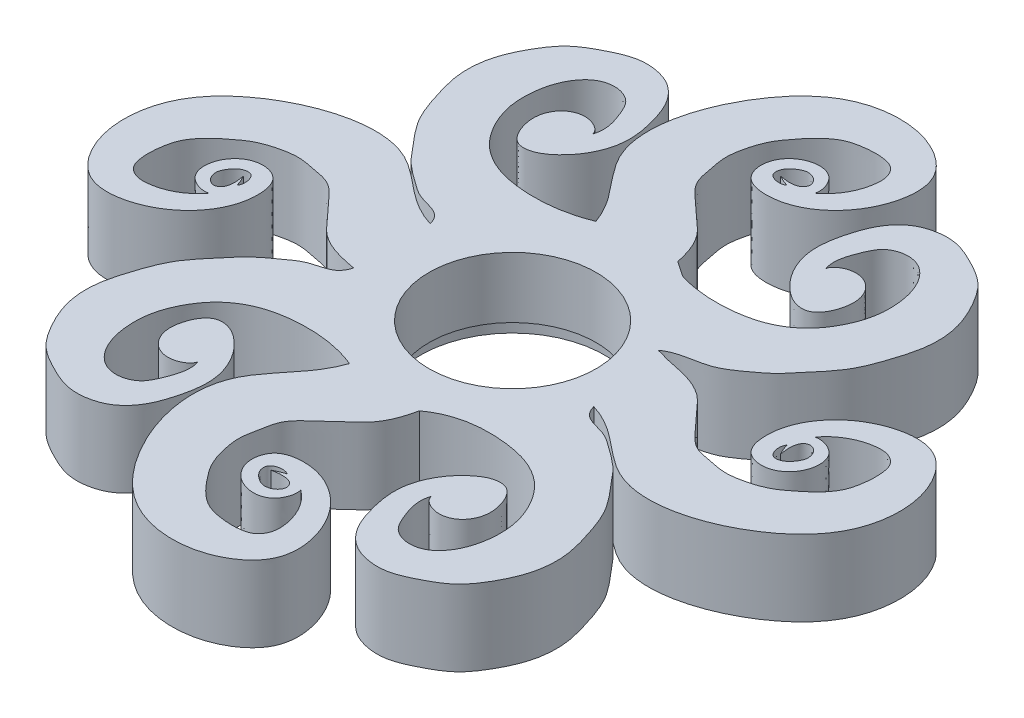
SolidWorks part; units mm, degrees
ref_plane "Front Plane" through (0, 0, 0) normal (0, 0, 1) x (1, 0, 0)
ref_plane "Top Plane" through (0, 0, 0) normal (0, 1, 0) x (1, 0, 0)
ref_plane "Right Plane" through (0, 0, 0) normal (1, 0, 0) x (0, 0, -1)
sketch "Sketch1" plane through (0, 0, 0) normal (0, 1, 0) x (1, 0, 0)
  line L0 (-137.5221, 312.9661) -> (42.0831, 492.5712) construction
  line L1 (0, 0) -> (100, 0)
  line L2 (0, 0) -> (0, 100)
  line L3 (0, 100) -> (100, 100)
  line L4 (100, 0) -> (100, 100)
  line L5 (0, 50) -> (100, 50) construction
  line L6 (50, 100) -> (50, 0) construction
  line L7 (0, 0) -> (100, 0)
  line L8 (0, 100) -> (100, 100)
  line L9 (0, 0) -> (100, 100)
  line L10 (0, 100) -> (100, 0)
  circle A0 centre (50, 50) radius 11
  spline S0 degree 3 poles (41.8661, 57.4054) (46.701, 61.1096) (45.1353, 68.2538) (35.8651, 77.0149) (39.534, 89.8969) (48.042, 98.1531) (57.0489, 98.3656) (63.2707, 93.2329) (62.2719, 86.5125) (58.4841, 81.8528) (53.9618, 80.0775) (49.6945, 80.8153) (48.8956, 84.5821) (51.2739, 87.369) (56.7979, 87.4647) (56.8692, 80.8999) (51.8214, 83.52) knots 0 0 0 0 0.130846 0.205908 0.373668 0.458524 0.563429 0.616002 0.684327 0.743989 0.794856 0.830051 0.857944 0.89521 0.928487 1 1 1 1
  spline S1 degree 3 poles (51.8214, 83.52) (52.472, 83.4079) (53.4015, 83.2628) (54.5829, 83.6983) (54.8837, 84.4198) (54.6621, 85.0586) (54.2169, 85.5067) (53.6439, 85.7228) (53.0512, 85.8036) (52.3837, 85.5614) (51.6885, 85.0892) (51.053, 84.3727) (50.8497, 82.6835) (52.804, 82.495) (53.2799, 82.9075) knots 0 0 0 0 0.166366 0.241726 0.299227 0.344909 0.407108 0.454045 0.499649 0.556761 0.630203 0.713357 0.798618 1 1 1 1
  spline S2 degree 3 poles (56.0389, 83.8395) (57.6208, 85.0131) (58.9873, 87.4073) (59.0345, 90.5343) (58.0896, 91.9736) (56.2517, 92.4492) (54.2472, 92.3528) (52.0283, 91.9307) (50.1178, 90.5672) (48.5985, 88.7801) (47.0469, 86.6832) (46.326, 84.3273) (45.9316, 81.9129) (46.4498, 79.6692) (46.8136, 77.1078) (48.8758, 75.2303) (50.9325, 73.3151) (53.6539, 71.081) (54.6991, 67.8956) (55.1151, 65.2419) (55.889, 63.2218) (55.1431, 59.3575) (58.2485, 58.4927) (59.1083, 56.1675) knots 0 0 0 0 0.103134 0.133672 0.160055 0.18614 0.228667 0.265873 0.302526 0.349029 0.389123 0.438157 0.476951 0.515573 0.558652 0.60831 0.655131 0.7086 0.789325 0.822647 0.849802 0.902946 1 1 1 1
  spline S3 degree 3 poles (56.0389, 16.1605) (57.6208, 14.9869) (58.9873, 12.5927) (59.0345, 9.4657) (58.0896, 8.0264) (56.2517, 7.5508) (54.2472, 7.6472) (52.0283, 8.0693) (50.1178, 9.4328) (48.5985, 11.2199) (47.0469, 13.3168) (46.326, 15.6727) (45.9316, 18.0871) (46.4498, 20.3308) (46.8136, 22.8922) (48.8758, 24.7697) (50.9325, 26.6849) (53.6539, 28.919) (54.6991, 32.1044) (55.1151, 34.7581) (55.889, 36.7782) (55.1431, 40.6425) (58.2485, 41.5073) (59.1083, 43.8325) knots 0 0 0 0 0.103134 0.133672 0.160055 0.18614 0.228667 0.265873 0.302526 0.349029 0.389123 0.438157 0.476951 0.515573 0.558652 0.60831 0.655131 0.7086 0.789325 0.822647 0.849802 0.902946 1 1 1 1
  spline S4 degree 3 poles (51.8214, 16.48) (52.472, 16.5921) (53.4015, 16.7372) (54.5829, 16.3017) (54.8837, 15.5802) (54.6621, 14.9414) (54.2169, 14.4933) (53.6439, 14.2772) (53.0512, 14.1964) (52.3837, 14.4386) (51.6885, 14.9108) (51.053, 15.6273) (50.8497, 17.3165) (52.804, 17.505) (53.2799, 17.0925) knots 0 0 0 0 0.166366 0.241726 0.299227 0.344909 0.407108 0.454045 0.499649 0.556761 0.630203 0.713357 0.798618 1 1 1 1
  spline S5 degree 3 poles (41.8661, 42.5946) (46.701, 38.8904) (45.1353, 31.7462) (35.8651, 22.9851) (39.534, 10.1031) (48.042, 1.8469) (57.0489, 1.6344) (63.2707, 6.7671) (62.2719, 13.4875) (58.4841, 18.1472) (53.9618, 19.9225) (49.6945, 19.1847) (48.8956, 15.4179) (51.2739, 12.631) (56.7979, 12.5353) (56.8692, 19.1001) (51.8214, 16.48) knots 0 0 0 0 0.130846 0.205908 0.373668 0.458524 0.563429 0.616002 0.684327 0.743989 0.794856 0.830051 0.857944 0.89521 0.928487 1 1 1 1
  spline S6 degree 3 poles (83.8395, 56.0389) (85.0131, 57.6208) (87.4073, 58.9873) (90.5343, 59.0345) (91.9736, 58.0896) (92.4492, 56.2517) (92.3528, 54.2472) (91.9307, 52.0283) (90.5672, 50.1178) (88.7801, 48.5985) (86.6832, 47.0469) (84.3273, 46.326) (81.9129, 45.9316) (79.6692, 46.4498) (77.1078, 46.8136) (75.2303, 48.8758) (73.3151, 50.9325) (71.081, 53.6539) (67.8956, 54.6991) (65.2419, 55.1151) (63.2218, 55.889) (59.3575, 55.1431) (58.4927, 58.2485) (56.1675, 59.1083) knots 0 0 0 0 0.103134 0.133672 0.160055 0.18614 0.228667 0.265873 0.302526 0.349029 0.389123 0.438157 0.476951 0.515573 0.558652 0.60831 0.655131 0.7086 0.789325 0.822647 0.849802 0.902946 1 1 1 1
  spline S7 degree 3 poles (83.52, 51.8214) (83.4079, 52.472) (83.2628, 53.4015) (83.6983, 54.5829) (84.4198, 54.8837) (85.0586, 54.6621) (85.5067, 54.2169) (85.7228, 53.6439) (85.8036, 53.0512) (85.5614, 52.3837) (85.0892, 51.6885) (84.3727, 51.053) (82.6835, 50.8497) (82.495, 52.804) (82.9075, 53.2799) knots 0 0 0 0 0.166366 0.241726 0.299227 0.344909 0.407108 0.454045 0.499649 0.556761 0.630203 0.713357 0.798618 1 1 1 1
  spline S8 degree 3 poles (57.4054, 41.8661) (61.1096, 46.701) (68.2538, 45.1353) (77.0149, 35.8651) (89.8969, 39.534) (98.1531, 48.042) (98.3656, 57.0489) (93.2329, 63.2707) (86.5125, 62.2719) (81.8528, 58.4841) (80.0775, 53.9618) (80.8153, 49.6945) (84.5821, 48.8956) (87.369, 51.2739) (87.4647, 56.7979) (80.8999, 56.8692) (83.52, 51.8214) knots 0 0 0 0 0.130846 0.205908 0.373668 0.458524 0.563429 0.616002 0.684327 0.743989 0.794856 0.830051 0.857944 0.89521 0.928487 1 1 1 1
  spline S9 degree 3 poles (16.1605, 43.9611) (14.9869, 42.3792) (12.5927, 41.0127) (9.4657, 40.9655) (8.0264, 41.9104) (7.5508, 43.7483) (7.6472, 45.7528) (8.0693, 47.9717) (9.4328, 49.8822) (11.2199, 51.4015) (13.3168, 52.9531) (15.6727, 53.674) (18.0871, 54.0684) (20.3308, 53.5502) (22.8922, 53.1864) (24.7697, 51.1242) (26.6849, 49.0675) (28.919, 46.3461) (32.1044, 45.3009) (34.7581, 44.8849) (36.7782, 44.111) (40.6425, 44.8569) (41.5073, 41.7515) (43.8325, 40.8917) knots 0 0 0 0 0.103134 0.133672 0.160055 0.18614 0.228667 0.265873 0.302526 0.349029 0.389123 0.438157 0.476951 0.515573 0.558652 0.60831 0.655131 0.7086 0.789325 0.822647 0.849802 0.902946 1 1 1 1
  spline S10 degree 3 poles (16.48, 48.1786) (16.5921, 47.528) (16.7372, 46.5985) (16.3017, 45.4171) (15.5802, 45.1163) (14.9414, 45.3379) (14.4933, 45.7831) (14.2772, 46.3561) (14.1964, 46.9488) (14.4386, 47.6163) (14.9108, 48.3115) (15.6273, 48.947) (17.3165, 49.1503) (17.505, 47.196) (17.0925, 46.7201) knots 0 0 0 0 0.166366 0.241726 0.299227 0.344909 0.407108 0.454045 0.499649 0.556761 0.630203 0.713357 0.798618 1 1 1 1
  spline S11 degree 3 poles (42.5946, 58.1339) (38.8904, 53.299) (31.7462, 54.8647) (22.9851, 64.1349) (10.1031, 60.466) (1.8469, 51.958) (1.6344, 42.9511) (6.7671, 36.7293) (13.4875, 37.7281) (18.1472, 41.5159) (19.9225, 46.0382) (19.1847, 50.3055) (15.4179, 51.1044) (12.631, 48.7261) (12.5353, 43.2021) (19.1001, 43.1308) (16.48, 48.1786) knots 0 0 0 0 0.130846 0.205908 0.373668 0.458524 0.563429 0.616002 0.684327 0.743989 0.794856 0.830051 0.857944 0.89521 0.928487 1 1 1 1
  spline S12 degree 3 poles (34.1884, 55.0434) (33.7016, 56.952) (30.9574, 56.8848) (28.119, 59.0296) (25.8782, 60.6685) (24.4047, 62.5739) (22.9411, 64.2057) (21.2354, 66.5202) (19.9851, 69.9916) (18.8891, 73.7521) (19.1559, 78.0048) (20.6589, 81.3054) (22.856, 84.5531) (25.899, 86.2636) (29.0199, 87.6795) (31.6929, 87.4706) (34.0752, 86.6383) (36.0255, 84.6259) (37.3044, 81.094) (38.2341, 76.3029) (36.0509, 72.3163) (33.8855, 70.5907) (32.6952, 69.8934) (30.9599, 69.6378) (29.7374, 70.891) (29.1677, 72.2055) (28.8482, 73.6602) (29.0518, 75.3626) (29.9773, 76.7405) (31.6842, 77.5967) (33.4225, 77.3986) (34.8521, 76.2044) (34.4451, 74.5803) (33.1722, 73.0823) (31.7022, 72.0226) (30.9569, 73.9879) knots 0 0 0 0 0.047267 0.084492 0.118113 0.141185 0.165634 0.192609 0.23794 0.28982 0.324183 0.379899 0.410854 0.455212 0.495953 0.524737 0.543497 0.580828 0.61431 0.670605 0.741153 0.752797 0.764261 0.788348 0.80436 0.819459 0.83697 0.854154 0.876413 0.889807 0.917327 0.931105 0.946423 0.966659 1 1 1 1
  spline S13 degree 3 poles (30.9569, 73.9879) (31.3845, 73.6785) (32.0299, 73.2113) (32.6853, 74.0624) (33.1102, 74.5719) (33.2738, 75.5172) (32.4237, 75.582) (31.7947, 75.4427) (31.327, 74.9826) (31.0485, 74.5027) (31.0389, 74.1446) (31.0336, 73.9436) knots 0 0 0 0 0.196597 0.29679 0.42697 0.538886 0.618953 0.750864 0.838714 0.909458 1 1 1 1
  spline S14 degree 3 poles (34.6468, 75.9336) (35.142, 77.3591) (34.4579, 79.442) (33.2298, 82.1516) (31.0419, 83.025) (28.7234, 82.5288) (26.7995, 80.4721) (25.7888, 77.1866) (25.8688, 73.6034) (27.1487, 70.3459) (29.1087, 67.5711) (32.2246, 65.6685) (37.6211, 64.5305) (41.9508, 65.0286) (44.8279, 66.2176) knots 0 0 0 0 0.099619 0.145832 0.199041 0.246529 0.301572 0.38394 0.478276 0.542636 0.623024 0.708169 0.787047 1 1 1 1
  spline S15 degree 3 poles (34.6468, 24.0664) (35.142, 22.6409) (34.4579, 20.558) (33.2298, 17.8484) (31.0419, 16.975) (28.7234, 17.4712) (26.7995, 19.5279) (25.7888, 22.8134) (25.8688, 26.3966) (27.1487, 29.6541) (29.1087, 32.4289) (32.2246, 34.3315) (37.6211, 35.4695) (41.9508, 34.9714) (44.8279, 33.7824) knots 0 0 0 0 0.099619 0.145832 0.199041 0.246529 0.301572 0.38394 0.478276 0.542636 0.623024 0.708169 0.787047 1 1 1 1
  spline S16 degree 3 poles (30.9569, 26.0121) (31.3845, 26.3215) (32.0299, 26.7887) (32.6853, 25.9376) (33.1102, 25.4281) (33.2738, 24.4828) (32.4237, 24.418) (31.7947, 24.5573) (31.327, 25.0174) (31.0485, 25.4973) (31.0389, 25.8554) (31.0336, 26.0564) knots 0 0 0 0 0.196597 0.29679 0.42697 0.538886 0.618953 0.750864 0.838714 0.909458 1 1 1 1
  spline S17 degree 3 poles (34.1884, 44.9566) (33.7016, 43.048) (30.9574, 43.1152) (28.119, 40.9704) (25.8782, 39.3315) (24.4047, 37.4261) (22.9411, 35.7943) (21.2354, 33.4798) (19.9851, 30.0084) (18.8891, 26.2479) (19.1559, 21.9952) (20.6589, 18.6946) (22.856, 15.4469) (25.899, 13.7364) (29.0199, 12.3205) (31.6929, 12.5294) (34.0752, 13.3617) (36.0255, 15.3741) (37.3044, 18.906) (38.2341, 23.6971) (36.0509, 27.6837) (33.8855, 29.4093) (32.6952, 30.1066) (30.9599, 30.3622) (29.7374, 29.109) (29.1677, 27.7945) (28.8482, 26.3398) (29.0518, 24.6374) (29.9773, 23.2595) (31.6842, 22.4033) (33.4225, 22.6014) (34.8521, 23.7956) (34.4451, 25.4197) (33.1722, 26.9177) (31.7022, 27.9774) (30.9569, 26.0121) knots 0 0 0 0 0.047267 0.084492 0.118113 0.141185 0.165634 0.192609 0.23794 0.28982 0.324183 0.379899 0.410854 0.455212 0.495953 0.524737 0.543497 0.580828 0.61431 0.670605 0.741153 0.752797 0.764261 0.788348 0.80436 0.819459 0.83697 0.854154 0.876413 0.889807 0.917327 0.931105 0.946423 0.966659 1 1 1 1
  spline S18 degree 3 poles (69.0431, 26.0121) (68.6155, 26.3215) (67.9701, 26.7887) (67.3147, 25.9376) (66.8898, 25.4281) (66.7262, 24.4828) (67.5763, 24.418) (68.2053, 24.5573) (68.673, 25.0174) (68.9515, 25.4973) (68.9611, 25.8554) (68.9664, 26.0564) knots 0 0 0 0 0.196597 0.29679 0.42697 0.538886 0.618953 0.750864 0.838714 0.909458 1 1 1 1
  spline S19 degree 3 poles (65.8116, 44.9566) (66.2984, 43.048) (69.0426, 43.1152) (71.881, 40.9704) (74.1218, 39.3315) (75.5953, 37.4261) (77.0589, 35.7943) (78.7646, 33.4798) (80.0149, 30.0084) (81.1109, 26.2479) (80.8441, 21.9952) (79.3411, 18.6946) (77.144, 15.4469) (74.101, 13.7364) (70.9801, 12.3205) (68.3071, 12.5294) (65.9248, 13.3617) (63.9745, 15.3741) (62.6956, 18.906) (61.7659, 23.6971) (63.9491, 27.6837) (66.1145, 29.4093) (67.3048, 30.1066) (69.0401, 30.3622) (70.2626, 29.109) (70.8323, 27.7945) (71.1518, 26.3398) (70.9482, 24.6374) (70.0227, 23.2595) (68.3158, 22.4033) (66.5775, 22.6014) (65.1479, 23.7956) (65.5549, 25.4197) (66.8278, 26.9177) (68.2978, 27.9774) (69.0431, 26.0121) knots 0 0 0 0 0.047267 0.084492 0.118113 0.141185 0.165634 0.192609 0.23794 0.28982 0.324183 0.379899 0.410854 0.455212 0.495953 0.524737 0.543497 0.580828 0.61431 0.670605 0.741153 0.752797 0.764261 0.788348 0.80436 0.819459 0.83697 0.854154 0.876413 0.889807 0.917327 0.931105 0.946423 0.966659 1 1 1 1
  spline S20 degree 3 poles (65.3532, 24.0664) (64.858, 22.6409) (65.5421, 20.558) (66.7702, 17.8484) (68.9581, 16.975) (71.2766, 17.4712) (73.2005, 19.5279) (74.2111, 22.8134) (74.1312, 26.3966) (72.8513, 29.6543) (70.8916, 32.428) (67.7742, 34.3349) (62.19, 35.4897) (57.5965, 35.0583) (54.8067, 32.9931) knots 0 0 0 0 0.098274 0.143863 0.196353 0.2432 0.297499 0.378754 0.471816 0.535307 0.614609 0.698604 0.776417 1 1 1 1
  spline S21 degree 1 poles (56.8387, 65.6495) (54.8067, 67.0069) knots 0 0 1 1
  spline S22 degree 1 poles (63.6193, 55.6152) (63.647, 55.6108) knots 0 0 1 1
  spline S24 degree 3 poles (69.0431, 73.9879) (68.6155, 73.6785) (67.9701, 73.2113) (67.3147, 74.0624) (66.8898, 74.5719) (66.7262, 75.5172) (67.5763, 75.582) (68.2053, 75.4427) (68.673, 74.9826) (68.9515, 74.5027) (68.9611, 74.1446) (68.9664, 73.9436) knots 0 0 0 0 0.196597 0.29679 0.42697 0.538886 0.618953 0.750864 0.838714 0.909458 1 1 1 1
  spline S25 degree 3 poles (65.3532, 75.9336) (64.858, 77.3591) (65.5421, 79.442) (66.7702, 82.1516) (68.9581, 83.025) (71.2766, 82.5288) (73.2005, 80.4721) (74.2112, 77.1866) (74.1312, 73.6034) (72.8513, 70.3459) (70.8913, 67.5712) (67.7753, 65.6682) (62.9562, 64.654) (59.2391, 64.9085) (56.8387, 65.6495) knots 0 0 0 0 0.103801 0.151955 0.207397 0.256879 0.314232 0.400058 0.498354 0.565416 0.649179 0.737898 0.820088 1 1 1 1
  spline S26 degree 3 poles (63.6193, 55.6152) (65.2177, 56.808) (68.5661, 56.6167) (71.8877, 59.0178) (74.1207, 60.6705) (75.5956, 62.5734) (77.0588, 64.2059) (78.7646, 66.5201) (80.0149, 69.9916) (81.1109, 73.7521) (80.8441, 78.0048) (79.3411, 81.3054) (77.144, 84.5531) (74.101, 86.2636) (70.9801, 87.6795) (68.3071, 87.4706) (65.9248, 86.6383) (63.9745, 84.6259) (62.6956, 81.094) (61.7659, 76.3029) (63.9491, 72.3163) (66.1145, 70.5907) (67.3048, 69.8934) (69.0401, 69.6378) (70.2626, 70.891) (70.8323, 72.2055) (71.1518, 73.6602) (70.9482, 75.3626) (70.0227, 76.7405) (68.3158, 77.5967) (66.5775, 77.3986) (65.1479, 76.2044) (65.5549, 74.5803) (66.8278, 73.0823) (68.2978, 72.0226) (69.0431, 73.9879) knots 0 0 0 0 0.06439 0.100946 0.133963 0.15662 0.18063 0.20712 0.251637 0.302584 0.336329 0.391044 0.421443 0.465004 0.505012 0.533278 0.551701 0.588362 0.621242 0.676525 0.745805 0.75724 0.768498 0.792152 0.807877 0.822703 0.8399 0.856775 0.878634 0.891787 0.918813 0.932343 0.947386 0.967258 1 1 1 1
  dimension "D3" = 22
  dimension "D1" = 100
  dimension "D2" = 100
extrude "Boss-Extrude2" add sketch "Sketch1" along normal blind 10
sketch "Sketch2" plane through (0, 0, 0) normal (0, 1, 0) x (1, 0, 0)
  line L6 (114.7807, 107.9462) -> (-12.1083, -9.8394) construction
  circle A0 centre (51.3362, 49.0534) radius 13.1665
  point P0 (51.3362, 49.0534)
extrude "Boss-Extrude4" add sketch "Sketch2" along normal blind 10
sketch "Sketch4" plane through (0, 10, 0) normal (0, 1, 0) x (1, 0, 0)
  circle A0 centre (50.657, 49.4232) radius 10.996
  dimension "D1" = 21.992
extrude "Cut-Extrude1" cut sketch "Sketch4" against normal blind 10
sketch "Sketch5" plane through (0, 0, 0) normal (0, 1, 0) x (1, 0, 0)
  line L0 (50.657, 60.4192) -> (50.657, 38.4272) construction
  line L1 (39.661, 49.4232) -> (61.653, 49.4232) construction
  circle A0 centre (50.657, 49.4232) radius 10.996 construction
  circle A1 centre (50.657, 49.4232) radius 12.126
  dimension "D1" = 24.252
extrude "Cut-Extrude2" cut sketch "Sketch5" along normal blind 2
